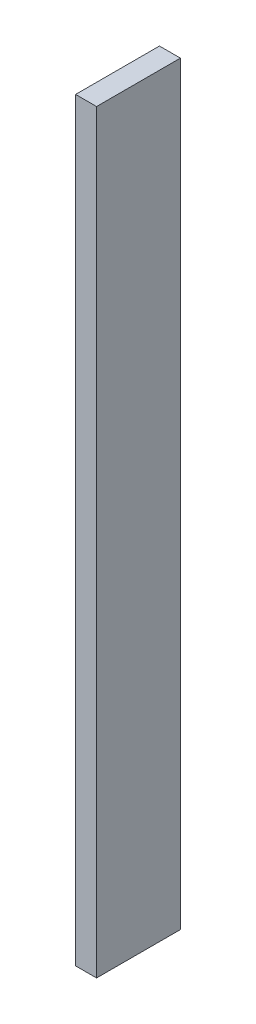
SolidWorks part; units mm, degrees
ref_plane "Front Plane" through (0, 0, 0) normal (0, 0, 1) x (1, 0, 0)
ref_plane "Top Plane" through (0, 0, 0) normal (0, 1, 0) x (1, 0, 0)
ref_plane "Right Plane" through (0, 0, 0) normal (1, 0, 0) x (0, 0, -1)
sketch "Sketch1" plane through (0, 0, 0) normal (0, 1, 0) x (1, 0, 0)
  line L1 (0, 0) -> (12.7, 0)
  line L2 (0, 0) -> (0, 50.8)
  line L3 (0, 50.8) -> (12.7, 50.8)
  line L4 (12.7, 0) -> (12.7, 50.8)
  dimension "D1" = 50.8
  dimension "D2" = 12.7
extrude "Boss-Extrude1" add sketch "Sketch1" against normal blind 457.2
